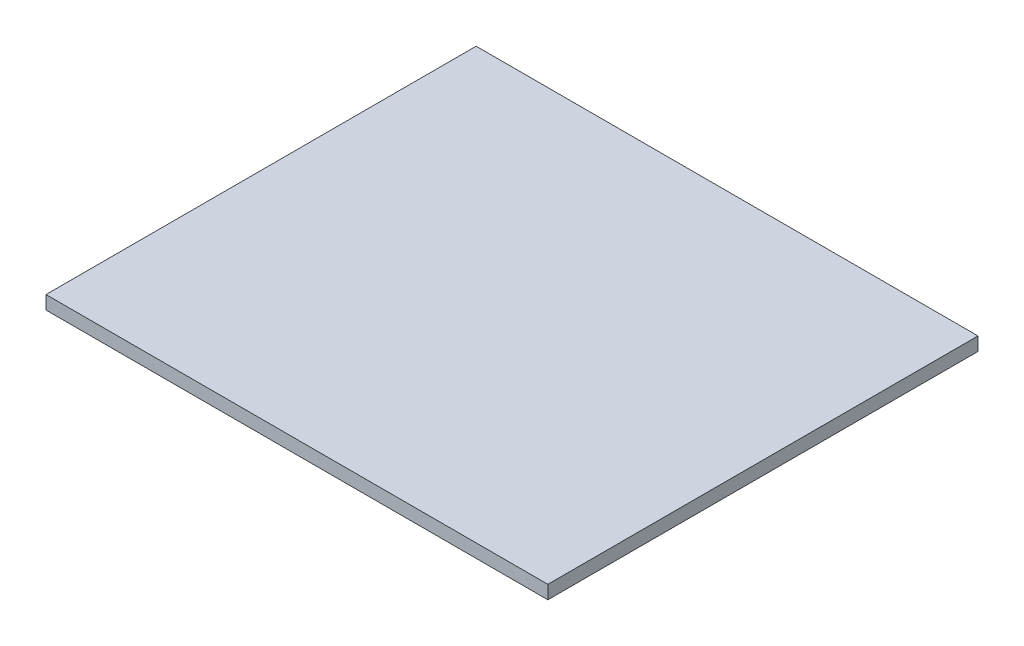
SolidWorks part; units mm, degrees
ref_plane "Front Plane" through (0, 0, 0) normal (0, 0, 1) x (1, 0, 0)
ref_plane "Top Plane" through (0, 0, 0) normal (0, 1, 0) x (1, 0, 0)
ref_plane "Right Plane" through (0, 0, 0) normal (1, 0, 0) x (0, 0, -1)
sketch "Sketch1" plane through (0, 0, 0) normal (0, 1, 0) x (1, 0, 0)
  line L1 (-355.6, -304.8) -> (355.6, -304.8)
  line L2 (-355.6, -304.8) -> (-355.6, 304.8)
  line L3 (-355.6, 304.8) -> (355.6, 304.8)
  line L4 (355.6, -304.8) -> (355.6, 304.8)
  line L5 (-355.6, -304.8) -> (355.6, 304.8) construction
  line L6 (-355.6, 304.8) -> (355.6, -304.8) construction
  point P0 (0, 0)
  dimension "D1" = 711.2
  dimension "D2" = 609.6
extrude "Boss-Extrude1" add sketch "Sketch1" along normal blind 19.05
